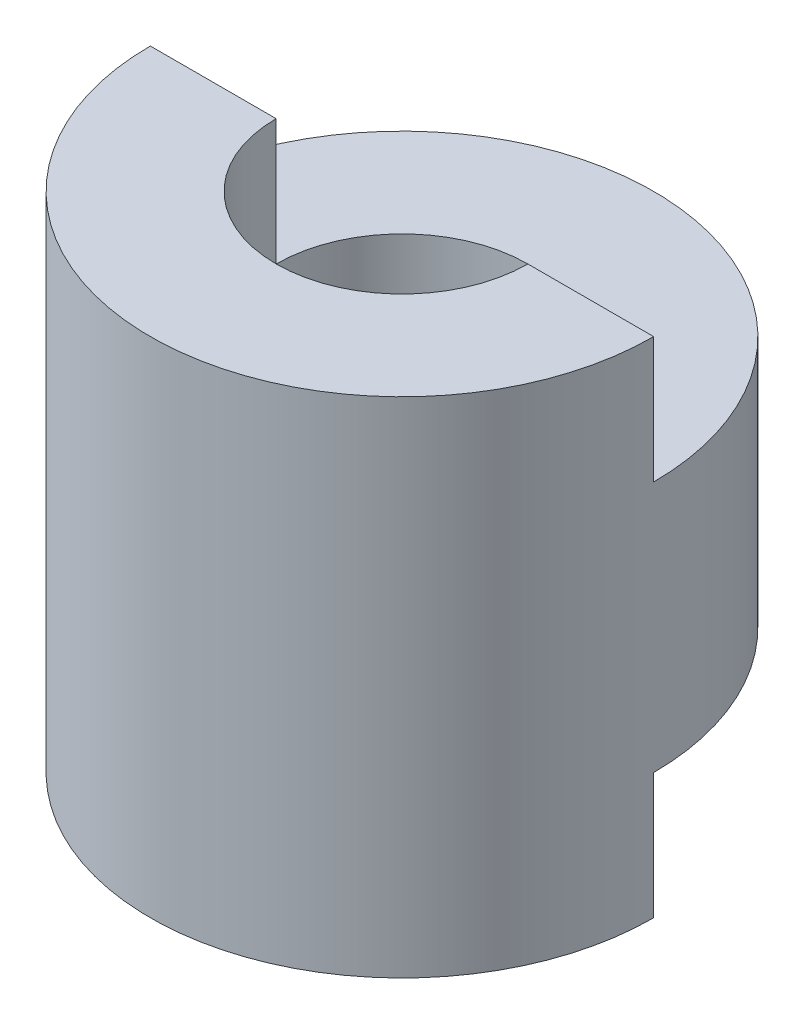
SolidWorks part; units mm, degrees
ref_plane "Front Plane" through (0, 0, 0) normal (0, 0, 1) x (1, 0, 0)
ref_plane "Top Plane" through (0, 0, 0) normal (0, 1, 0) x (1, 0, 0)
ref_plane "Right Plane" through (0, 0, 0) normal (1, 0, 0) x (0, 0, -1)
sketch "Sketch1" plane through (0, 0, 0) normal (0, 0, 1) x (1, 0, 0)
  line L1 (0, 0) -> (10, 0)
  line L2 (0, 0) -> (0, 20)
  line L3 (0, 20) -> (10, 20)
  line L4 (10, 0) -> (10, 20)
  dimension "D1" = 20
  dimension "D2" = 10
revolve "Revolve1" add sketch "Sketch1" angle 360 about L2
sketch "Sketch2" plane through (0, 20, 0) normal (0, 1, 0) x (1, 0, 0)
  circle A0 centre (0, 0) radius 5
  dimension "D1" = 10
extrude "Cut-Extrude1" cut sketch "Sketch2" against normal blind 20
sketch "Sketch3" plane through (0, 20, 0) normal (0, 1, 0) x (1, 0, 0)
  line L0 (-10, 0) -> (-5, 0)
  line L1 (5, 0) -> (10, 0)
  arc A0 (-10, 0) -> (10, 0) centre (0, 0) cw
  circle A1 centre (0, 0) radius 10 construction
  arc A2 (-5, 0) -> (5, 0) centre (0, 0) cw
  circle A3 centre (0, 0) radius 5 construction
  dimension "D3" = 5
  dimension "D4" = 10
  dimension "D1" = 5
  dimension "D2" = 5
extrude "Cut-Extrude2" cut sketch "Sketch3" against normal blind 5
sketch "Sketch4" plane through (0, 0, 0) normal (0, -1, 0) x (1, 0, 0)
  line L0 (-10, 0) -> (-5, 0)
  line L1 (5, 0) -> (10, 0)
  arc A0 (-10, 0) -> (10, 0) centre (0, 0) ccw
  arc A1 (-5, 0) -> (5, 0) centre (0, 0) ccw
  dimension "D1" = 5
  dimension "D2" = 10
extrude "Cut-Extrude3" cut sketch "Sketch4" against normal blind 5
